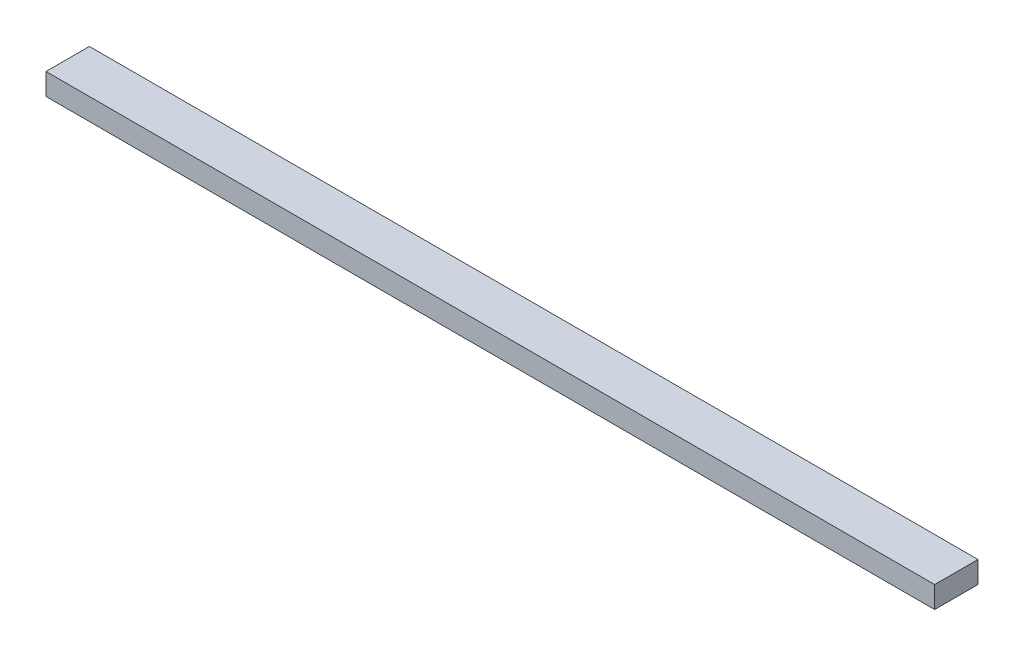
SolidWorks part; units mm, degrees
ref_plane "Front Plane" through (0, 0, 0) normal (0, 0, 1) x (1, 0, 0)
ref_plane "Top Plane" through (0, 0, 0) normal (0, 1, 0) x (1, 0, 0)
ref_plane "Right Plane" through (0, 0, 0) normal (1, 0, 0) x (0, 0, -1)
sketch "Sketch1" plane through (0, 0, 0) normal (0, 1, 0) x (1, 0, 0)
  line L0 (-205, 10) -> (205, -10) construction
  line L1 (-205, 10) -> (205, 10)
  line L2 (-205, 10) -> (-205, -10)
  line L3 (-205, -10) -> (205, -10)
  line L4 (205, 10) -> (205, -10)
  dimension "D1" = 410
  dimension "D2" = 20
extrude "Boss-Extrude1" add sketch "Sketch1" along normal blind 10
